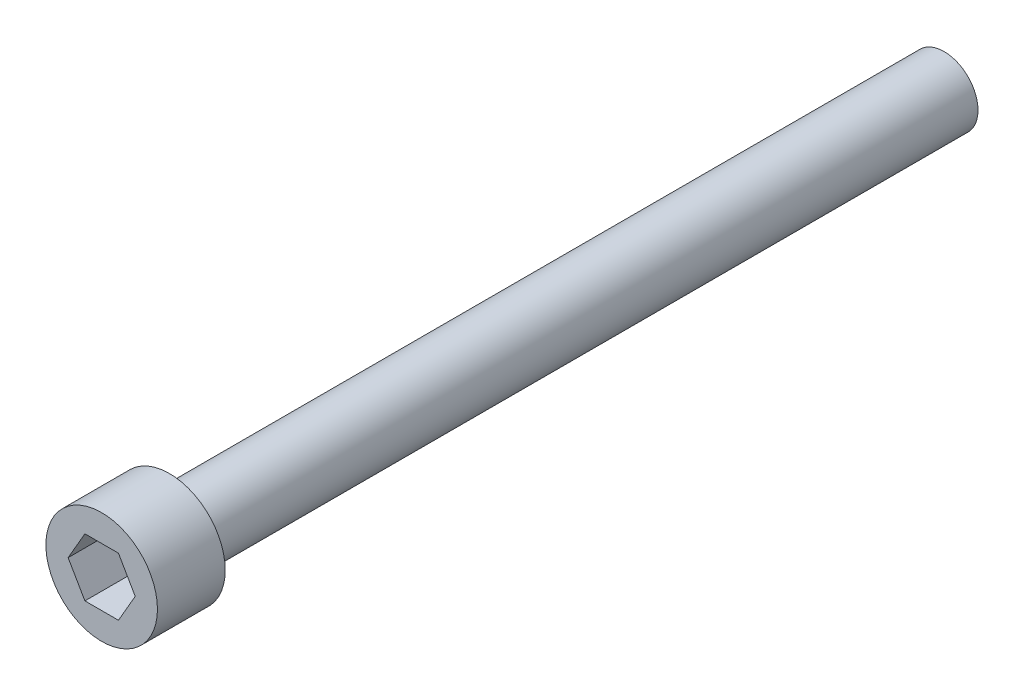
SolidWorks part; units mm, degrees
material "AISI 4340 Steel, normalized"
ref_plane "Front Plane" through (0, 0, 0) normal (0, 0, 1) x (1, 0, 0)
ref_plane "Top Plane" through (0, 0, 0) normal (0, 1, 0) x (1, 0, 0)
ref_plane "Right Plane" through (0, 0, 0) normal (1, 0, 0) x (0, 0, -1)
sketch "Sketch1" plane through (0, 0, 0) normal (0, 1, 0) x (1, 0, 0)
  line L0 (0, 0) -> (0, 51.7906)
  line L1 (0, 51.7906) -> (2.0828, 51.7906)
  line L2 (2.0828, 51.7906) -> (2.0828, 4.1656)
  line L3 (2.0828, 4.1656) -> (3.429, 4.1656)
  line L4 (3.429, 4.1656) -> (3.429, 0)
  line L5 (3.429, 0) -> (0, 0)
  dimension "D1" = 2.0828
  dimension "D2" = 3.429
  dimension "D3" = 4.1656
  dimension "D4" = 47.625
revolve "Revolve1" add sketch "Sketch1" angle 360 about L0
sketch "Sketch2" plane through (0, 0, 0) normal (0, 0, 1) x (1, 0, 0)
  line L1 (2.0622, 0) -> (1.0311, 1.7859)
  line L2 (1.0311, 1.7859) -> (-1.0311, 1.7859)
  line L3 (-1.0311, 1.7859) -> (-2.0622, 0)
  line L4 (-2.0622, 0) -> (-1.0311, -1.7859)
  line L5 (-1.0311, -1.7859) -> (1.0311, -1.7859)
  line L6 (1.0311, -1.7859) -> (2.0622, 0)
  circle A0 centre (0, 0) radius 1.7859 construction
  dimension "D1" = 3.5719
extrude "9-64 allen" cut sketch "Sketch2" against normal blind 3.175
